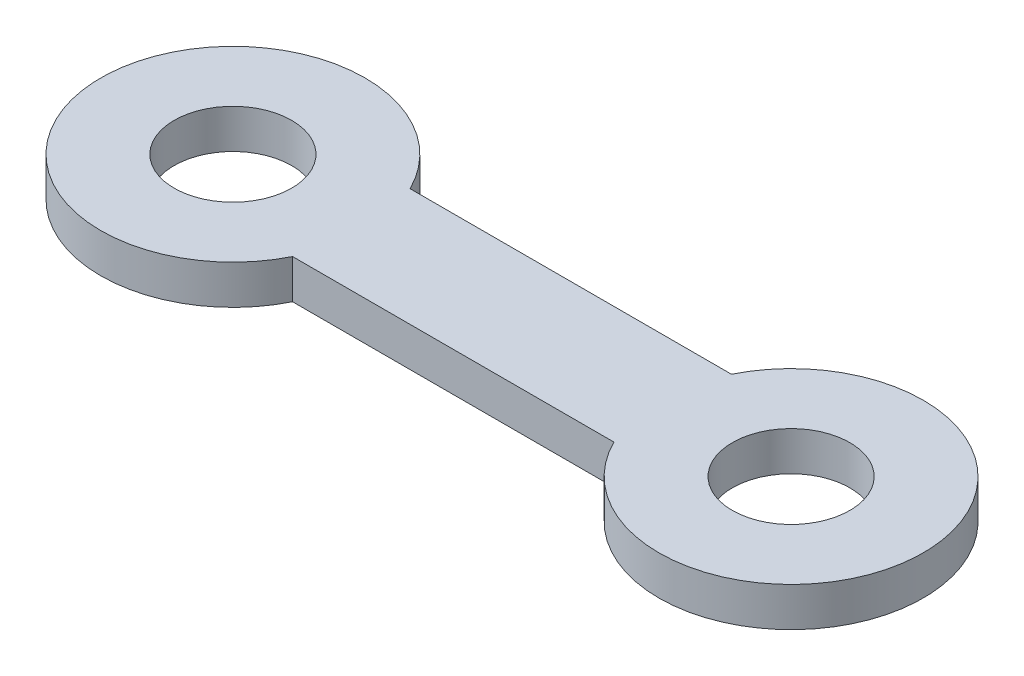
SolidWorks part; units mm, degrees
material "1060 Alloy"
ref_plane "Front" through (0, 0, 0) normal (0, 0, 1) x (1, 0, 0)
ref_plane "Top" through (0, 0, 0) normal (0, 1, 0) x (1, 0, 0)
ref_plane "Right" through (0, 0, 0) normal (1, 0, 0) x (0, 0, -1)
sketch "Sketch1" plane through (0, 0, 0) normal (0, 1, 0) x (1, 0, 0)
  line L0 (-3.0233, 1.5) -> (-11.2267, 1.5)
  line L1 (-7.125, 1.5) -> (-7.125, -1.5) construction
  line L2 (-11.2267, -1.5) -> (-3.0233, -1.5)
  circle A0 centre (0, 0) radius 1.5
  arc A1 (-3.0233, -1.5) -> (-3.0233, 1.5) centre (0, 0) ccw
  circle A2 centre (-14.25, 0) radius 1.5
  arc A3 (-11.2267, -1.5) -> (-11.2267, 1.5) centre (-14.25, 0) cw
  point P8 (-7.125, 0)
  dimension "D1" = 3
  dimension "D2" = 6.75
  dimension "D4" = 21
  dimension "D3" = 3
extrude "Boss-Extrude1" add sketch "Sketch1" along normal blind 1
